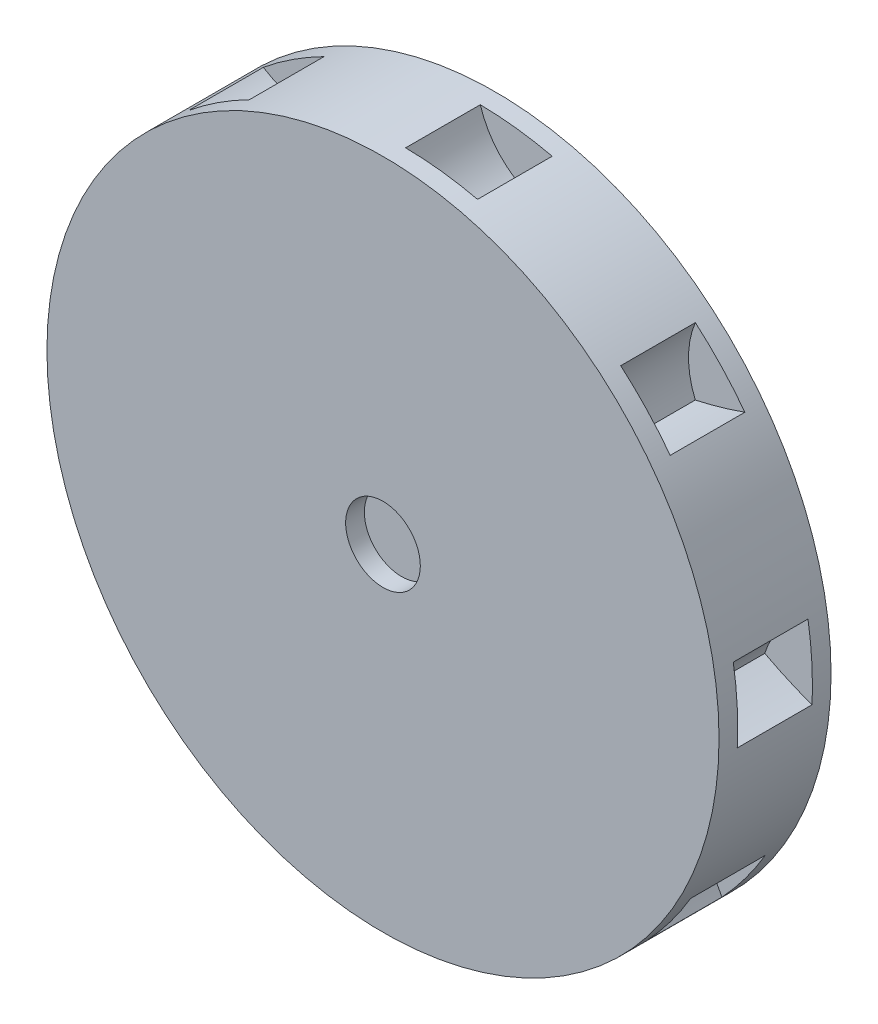
SolidWorks part; units mm, degrees
ref_plane "Front Plane" through (0, 0, 0) normal (0, 0, 1) x (1, 0, 0)
ref_plane "Top Plane" through (0, 0, 0) normal (0, 1, 0) x (1, 0, 0)
ref_plane "Right Plane" through (0, 0, 0) normal (1, 0, 0) x (0, 0, -1)
sketch "Sketch1" plane through (0, 0, 0) normal (0, 0, 1) x (1, 0, 0)
  circle A0 centre (0, 0) radius 45
  circle A1 centre (0, 0) radius 5
  dimension "D1" = 90
  dimension "D2" = 10
extrude "Boss-Extrude1" add sketch "Sketch1" along normal blind 2.5
sketch "Sketch2" plane through (0, 0, 0) normal (0, 0, -1) x (-1, 0, 0)
  line L1 (2.3769, 27.9193) -> (2.9968, 28.704)
  arc A0 (2.3769, 27.9193) -> (-11.1734, 43.5908) centre (36.4998, 71.1177) cw
  arc A1 (2.9968, 28.704) -> (-5.694, 37.3381) centre (36.4998, 71.1177) cw
  arc A2 (0.4729, 44.9975) -> (-5.694, 37.3381) centre (-11.5621, 48.3751) cw
  circle A3 centre (0, 0) radius 45 construction
  arc A4 (-6.2983, 38.1072) -> (-0.5293, 44.9969) centre (-11.5621, 48.3751) ccw
  arc A5 (-6.2983, 38.1072) -> (-10.1605, 43.8379) centre (36.4998, 71.1177) cw
  arc A6 (2.9968, 28.704) -> (-13.7695, 51.2591) centre (36.4998, 71.1177) cw construction
  arc A7 (0.4729, 44.9975) -> (-0.5293, 44.9969) centre (0, 0) ccw
  arc A9 (2.3769, 27.9193) -> (-14.6996, 50.8916) centre (36.4998, 71.1177) cw construction
  arc A10 (-10.1605, 43.8379) -> (-11.1734, 43.5908) centre (0, 0) ccw
  dimension "D1" = 11.5385
  dimension "D2" = 12.5
extrude "Boss-Extrude2" add sketch "Sketch2" along normal blind 10
pattern_circular "CirPattern3" count 9 over 360 about axis through (0, 0, 0) along (0, 0, 1) of "Boss-Extrude2"
sketch "Sketch3" plane through (0, 0, 0) normal (0, 0, -1) x (-1, 0, 0)
  arc A0 (0.1454, 43.9951) -> (19.2883, 39.5418) centre (0, 0) cw
  arc A1 (-5.694, 37.3381) -> (0.4729, 44.9975) centre (-11.5621, 48.3751) ccw construction
  arc A2 (0.1454, 43.9951) -> (0.4729, 44.9975) centre (-11.5621, 48.3751) ccw
  arc A3 (0.4729, 44.9975) -> (19.4602, 40.5746) centre (0, 0) cw
  arc A4 (19.4602, 40.5746) -> (19.2883, 39.5418) centre (73.674, 31.0177) ccw
ref_plane "Plane1" through (0, 0, -5) normal (0, 0, 1) x (1, 0, 0)
extrude "Boss-Extrude6" add sketch "Sketch3" along normal blind 10
pattern_circular "CirPattern4" count 9 over 360 about axis through (0, 0, 2.5) along (0, 0, -1) of "Boss-Extrude6"
mirror "Mirror3" about plane through (0, 0, -5) normal (0, 0, 1) of "Boss-Extrude1"
